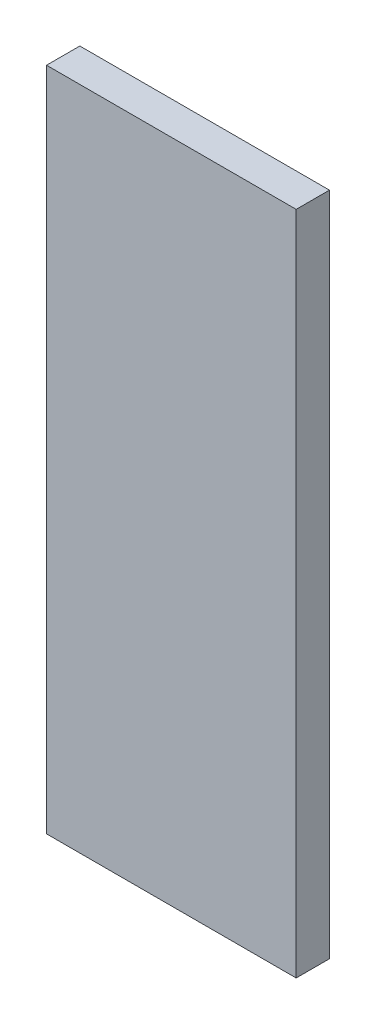
SolidWorks part; units mm, degrees
material "6061-T6 (SS)"
ref_plane "Alzado" through (0, 0, 0) normal (0, 0, 1) x (1, 0, 0)
ref_plane "Planta" through (0, 0, 0) normal (0, 1, 0) x (1, 0, 0)
ref_plane "Vista lateral" through (0, 0, 0) normal (1, 0, 0) x (0, 0, -1)
sketch "Sketch1" plane through (0, 0, 0) normal (0, 0, 1) x (1, 0, 0)
  line L1 (-15, 40) -> (15, 40)
  line L2 (-15, 40) -> (-15, -40)
  line L3 (-15, -40) -> (15, -40)
  line L4 (15, 40) -> (15, -40)
  line L5 (-15, 40) -> (15, -40) construction
  line L6 (-15, -40) -> (15, 40) construction
  point P0 (0, 0)
  dimension "D1" = 30
  dimension "D2" = 80
extrude "Boss-Extrude1" add sketch "Sketch1" along normal blind 4
